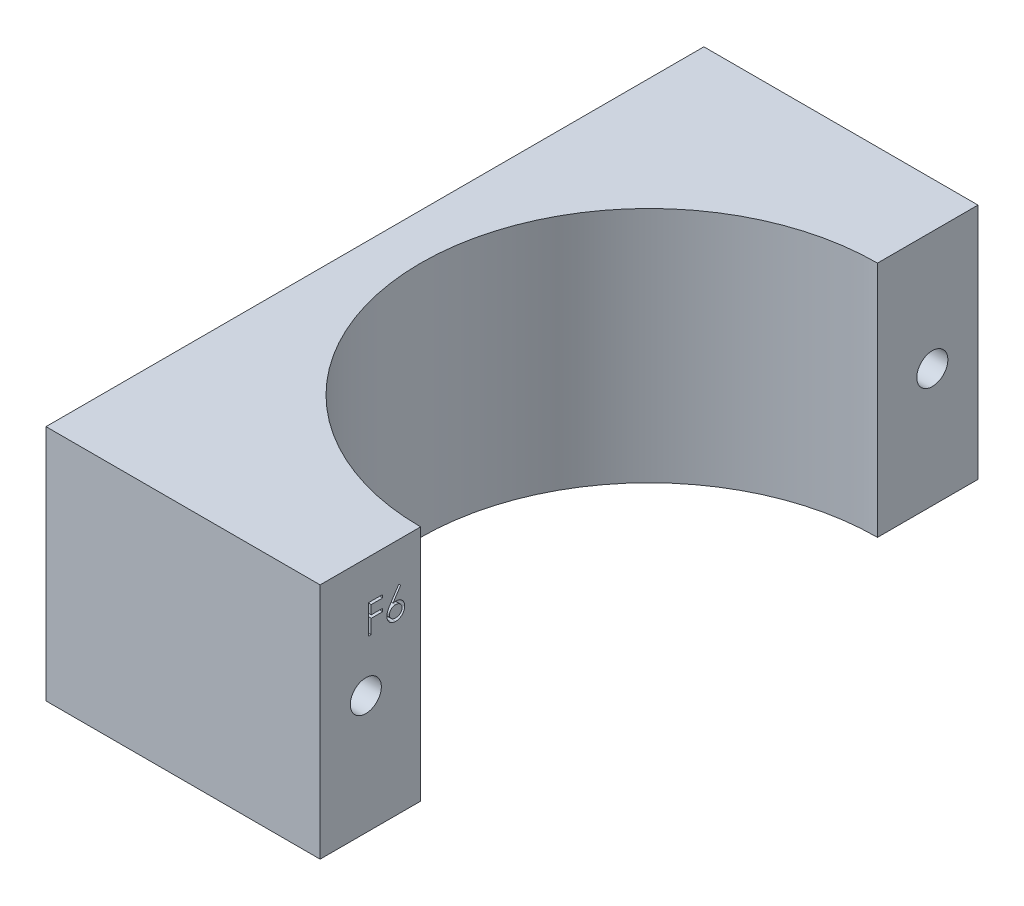
SolidWorks part; units mm, degrees
ref_plane "Front Plane" through (0, 0, 0) normal (0, 0, 1) x (1, 0, 0)
ref_plane "Top Plane" through (0, 0, 0) normal (0, 1, 0) x (1, 0, 0)
ref_plane "Right Plane" through (0, 0, 0) normal (1, 0, 0) x (0, 0, -1)
sketch "Sketch1" plane through (0, 0, 0) normal (0, 1, 0) x (1, 0, 0)
  line L0 (-46.9983, 32.5286) -> (-46.9983, -39.4714)
  line L1 (-46.9983, -39.4714) -> (-16.9983, -39.4714)
  line L2 (-16.9983, -39.4714) -> (-16.9983, -28.4714)
  line L3 (-46.9983, 32.5286) -> (-16.9983, 32.5286)
  line L4 (-16.9983, 32.5286) -> (-16.9983, 21.5286)
  arc A0 (-16.9983, 21.5286) -> (-16.9983, -28.4714) centre (-16.9983, -3.4714) ccw
  dimension "D1" = 72
  dimension "D2" = 30
  dimension "D3" = 30
  dimension "D4" = 11
  dimension "D5" = 11
extrude "Boss-Extrude1" add sketch "Sketch1" along normal blind 26
sketch "Sketch2" plane through (-16.9983, 0, 0) normal (1, 0, 0) x (0, 0, -1)
  line L0 (-34.4714, 26) -> (-34.4714, 0) construction
  line L1 (-39.4714, 26) -> (-28.4714, 26) construction
  line L2 (-39.4714, 0) -> (-28.4714, 0) construction
  line L3 (27.5286, 26) -> (27.5286, 0) construction
  line L4 (21.5286, 26) -> (32.5286, 26) construction
  line L5 (21.5286, 0) -> (32.5286, 0) construction
  line L6 (-39.4714, 26) -> (-39.4714, 0) construction
  line L7 (32.5286, 26) -> (32.5286, 0) construction
  circle A0 centre (-34.4714, 13) radius 1.7
  circle A1 centre (27.5286, 13) radius 1.7
  dimension "D1" = 5
  dimension "D2" = 5
extrude "Cut-Extrude1" cut sketch "Sketch2" against normal through all
sketch "Sketch3" plane through (-16.9983, 0, 0) normal (1, 0, 0) x (0, 0, -1)
  text T0 "F6"
extrude "Cut-Extrude2" cut sketch "Sketch3" against normal blind 1
